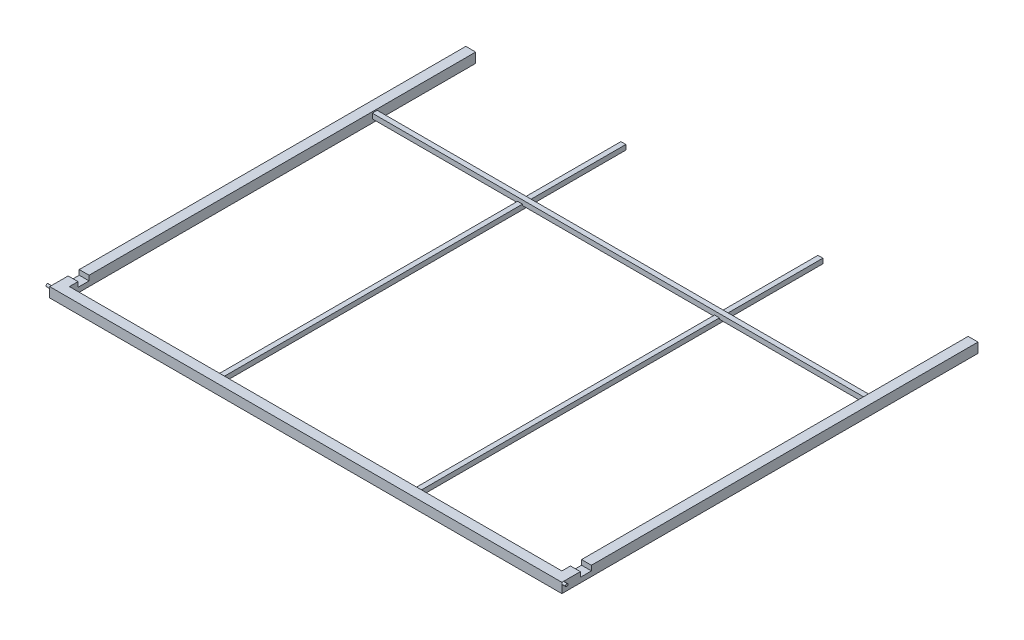
SolidWorks part; units mm, degrees
material "2014-T4"
ref_plane "Front Plane" through (0, 0, 0) normal (0, 0, 1) x (1, 0, 0)
ref_plane "Top Plane" through (0, 0, 0) normal (0, 1, 0) x (1, 0, 0)
ref_plane "Right Plane" through (0, 0, 0) normal (1, 0, 0) x (0, 0, -1)
sketch "Sketch1" plane through (0, 0, 0) normal (0, 1, 0) x (1, 0, 0)
  line L0 (1308.1, -1066.8) -> (1308.1, 1066.8)
  line L2 (-1308.1, 1066.8) -> (-1308.1, -1066.8)
  line L3 (-1308.1, -1066.8) -> (1308.1, -1066.8)
  line L5 (-1308.1, 1066.8) -> (1308.1, -1066.8) construction
  line L6 (-1308.1, -1066.8) -> (1308.1, 1066.8) construction
  point P0 (0, 0)
  dimension "D1" = 2133.6
  dimension "D2" = 2616.2
sketch "Sketch2" plane through (0, 0, 0) normal (0, 0, 1) x (1, 0, 0)
  line L0 (-1308.1, 0) -> (1308.1, 0) construction
  line L1 (-1320.8, 25.4) -> (-1270, 25.4)
  line L2 (-1320.8, 25.4) -> (-1320.8, -25.4)
  line L3 (-1320.8, -25.4) -> (-1270, -25.4)
  line L4 (-1270, 25.4) -> (-1270, -25.4)
  line L5 (-1320.8, 25.4) -> (-1270, -25.4) construction
  line L6 (-1320.8, -25.4) -> (-1270, 25.4) construction
  line L7 (-1308.1, 0) -> (1308.1, 0) construction
  line L8 (-1273.175, 22.225) -> (-1273.175, -22.225)
  line L9 (-1317.625, -22.225) -> (-1273.175, -22.225)
  line L10 (-1317.625, 22.225) -> (-1317.625, -22.225)
  line L11 (-1317.625, 22.225) -> (-1273.175, 22.225)
  point P0 (-1295.4, 0)
  dimension "D1" = 50.8
  dimension "D2" = 50.8
  dimension "D4" = 1295.4
  dimension "D3" = 3.175
sweep "Sweep1" add profiles "Sketch2" path "Sketch1"
sketch "Sketch6" plane through (-1320.8, 0, 0) normal (-1, 0, 0) x (0, 0, 1)
  line L1 (1079.5, 25.4) -> (-1066.8, 25.4) construction
  line L2 (1079.5, -25.4) -> (1079.5, 25.4) construction
  circle A0 centre (1073.15, 19.05) radius 6.35
  dimension "D3" = 12.7
  dimension "D1" = 6.35
  dimension "D2" = 6.35
extrude "Boss-Extrude3" add sketch "Sketch6" along normal blind 19.05
sketch "Sketch12" plane through (1320.8, 0, 0) normal (1, 0, 0) x (0, 0, -1)
  line L0 (-1079.5, -25.4) -> (-1079.5, 25.4) construction
  line L1 (-1079.5, 25.4) -> (1066.8, 25.4) construction
  circle A0 centre (-1073.15, 19.05) radius 6.35
  dimension "D1" = 12.7
extrude "Boss-Extrude6" add sketch "Sketch12" along normal blind 19.05 contours A0
ref_plane "Plane1" through (0, 0, 1073.15) normal (0, 0, 1) x (1, 0, 0)
sketch "Sketch7" plane through (0, 0, 1073.15) normal (0, 0, 1) x (1, 0, 0)
  line L0 (1422.4, 19.05) -> (-1422.4, 19.05) construction
  line L1 (-1320.8, -25.4) -> (-1320.8, 19.05) construction
  line L2 (1320.8, -25.4) -> (1320.8, 19.05) construction
  dimension "D1" = 6.35
  dimension "D2" = 101.6
  dimension "D3" = 101.6
sketch "Sketch13" plane through (-1320.8, 0, 0) normal (-1, 0, 0) x (0, 0, 1)
  line L0 (-1066.8, 25.4) -> (1073.15, 25.4) construction
  line L1 (927.1, 25.4) -> (984.25, 25.4)
  line L2 (927.1, 25.4) -> (927.1, 0)
  line L3 (927.1, 0) -> (984.25, 0)
  line L4 (984.25, 25.4) -> (984.25, 0)
  line L5 (927.1, 25.4) -> (984.25, 0) construction
  line L6 (927.1, 0) -> (984.25, 25.4) construction
  line L7 (1079.5, -25.4) -> (1079.5, 19.05) construction
  point P0 (955.675, 12.7)
  dimension "D1" = 57.15
  dimension "D2" = 25.4
  dimension "D3" = 152.4
extrude "Cut-Extrude2" cut sketch "Sketch13" against normal up to surface (2641.6 mm away) up to face at (1320.8, 2.277, 218.177)
sketch "Sketch14" plane through (1270, 0, 0) normal (-1, 0, 0) x (0, 0, 1)
  line L1 (-558.8, 19.05) -> (-533.4, 19.05)
  line L2 (-558.8, 19.05) -> (-558.8, -6.35)
  line L3 (-558.8, -6.35) -> (-533.4, -6.35)
  line L4 (-533.4, 19.05) -> (-533.4, -6.35)
  line L5 (-558.8, 19.05) -> (-533.4, -6.35) construction
  line L6 (-558.8, -6.35) -> (-533.4, 19.05) construction
  line L7 (-1066.8, -25.4) -> (-1066.8, 25.4) construction
  line L8 (-555.625, 15.875) -> (-555.625, -3.175)
  line L9 (-555.625, -3.175) -> (-536.575, -3.175)
  line L10 (-536.575, 15.875) -> (-536.575, -3.175)
  line L11 (-555.625, 15.875) -> (-536.575, 15.875)
  line L12 (1028.7, -25.4) -> (-1066.8, -25.4) construction
  point P0 (-546.1, 6.35)
  dimension "D1" = 25.4
  dimension "D2" = 25.4
  dimension "D3" = 508
  dimension "D5" = 19.05
  dimension "D4" = 3.175
extrude "Boss-Extrude7" add sketch "Sketch14" along normal up to surface (2540 mm away) separate body up to face at (-1270, 6.35, 468.3125)
sketch "Sketch16" plane through (0, 0, -558.8) normal (0, 0, -1) x (-1, 0, 0)
  line L0 (-1270, 19.05) -> (-1270, -6.35) construction
  line L1 (-520.7, 0) -> (-495.3, 0)
  line L2 (-520.7, 0) -> (-520.7, -6.35)
  line L3 (-520.7, -6.35) -> (-495.3, -6.35)
  line L4 (-495.3, 0) -> (-495.3, -6.35)
  line L5 (-520.7, 0) -> (-495.3, -6.35) construction
  line L6 (-520.7, -6.35) -> (-495.3, 0) construction
  line L7 (1270, -6.35) -> (-1270, -6.35) construction
  line L8 (495.3, 0) -> (495.3, -6.35)
  line L9 (495.3, 0) -> (520.7, 0)
  line L10 (520.7, 0) -> (520.7, -6.35)
  line L11 (495.3, -6.35) -> (520.7, -6.35)
  line L12 (1270, -6.35) -> (1270, 19.05) construction
  point P0 (-508, -3.175)
  point P9 (508, 0)
  dimension "D1" = 6.35
  dimension "D2" = 25.4
  dimension "D3" = 762
  dimension "D5" = 762
  dimension "D4" = 2
extrude "Cut-Extrude3" cut sketch "Sketch16" against normal up to surface (25.4 mm away) up to face at (0, 6.35, -533.4)
sketch "Sketch15" plane through (0, 0, 1028.7) normal (0, 0, -1) x (-1, 0, 0)
  line L0 (1270, -25.4) -> (-1270, -25.4) construction
  line L1 (-520.7, 0) -> (-495.3, 0)
  line L2 (-520.7, 0) -> (-520.7, -25.4)
  line L3 (-520.7, -25.4) -> (-495.3, -25.4)
  line L4 (-495.3, 0) -> (-495.3, -25.4)
  line L5 (-520.7, 0) -> (-495.3, -25.4) construction
  line L6 (-520.7, -25.4) -> (-495.3, 0) construction
  line L7 (-1270, 25.4) -> (-1270, -25.4) construction
  line L8 (-517.525, -3.175) -> (-517.525, -22.225)
  line L9 (-517.525, -22.225) -> (-498.475, -22.225)
  line L10 (-498.475, -3.175) -> (-498.475, -22.225)
  line L11 (-517.525, -3.175) -> (-498.475, -3.175)
  line L12 (498.475, -3.175) -> (498.475, -22.225)
  line L13 (498.475, -22.225) -> (517.525, -22.225)
  line L14 (517.525, -3.175) -> (517.525, -22.225)
  line L15 (498.475, -3.175) -> (517.525, -3.175)
  line L16 (495.3, 0) -> (495.3, -25.4)
  line L17 (495.3, 0) -> (520.7, 0)
  line L18 (520.7, 0) -> (520.7, -25.4)
  line L19 (495.3, -25.4) -> (520.7, -25.4)
  line L20 (1270, 25.4) -> (1270, -25.4) construction
  point P0 (-508, -12.7)
  point P23 (508, 0)
  dimension "D1" = 25.4
  dimension "D2" = 25.4
  dimension "D3" = 762
  dimension "D6" = 762
  dimension "D4" = 3.175
  dimension "D5" = 2
extrude "Boss-Extrude9" add sketch "Sketch15" along normal up to surface (2095.5 mm away) separate body up to face at (1295.4, 0, -1066.8)
sketch "Sketch17" plane through (1320.8, 0, 0) normal (1, 0, 0) x (0, 0, -1)
  line L0 (-984.25, 25.4) -> (-987.425, 25.4)
  line L1 (-1073.15, 25.4) -> (-984.25, 25.4) construction
  line L2 (-987.425, 25.4) -> (-987.425, -3.175)
  line L3 (-987.425, -3.175) -> (-923.925, -3.175)
  line L4 (-923.925, -3.175) -> (-923.925, 25.4)
  line L5 (-927.1, 25.4) -> (1066.8, 25.4) construction
  line L6 (-923.925, 25.4) -> (-927.1, 25.4)
  line L7 (-927.1, 25.4) -> (-927.1, 0)
  line L8 (-927.1, 0) -> (-984.25, 0)
  line L9 (-984.25, 0) -> (-984.25, 25.4)
  dimension "D1" = 3.175
  dimension "D2" = 3.175
  dimension "D3" = 3.175
extrude "Boss-Extrude10" add sketch "Sketch17" against normal up to surface (50.8 mm away) up to face at (1270, 6.35, 468.3125)
sketch "Sketch18" plane through (-1320.8, 0, 0) normal (-1, 0, 0) x (0, 0, 1)
  line L0 (927.1, 25.4) -> (923.925, 25.4)
  line L1 (-1066.8, 25.4) -> (927.1, 25.4) construction
  line L2 (923.925, 25.4) -> (923.925, -3.175)
  line L3 (923.925, -3.175) -> (987.425, -3.175)
  line L4 (987.425, -3.175) -> (987.425, 25.4)
  line L5 (984.25, 25.4) -> (1073.15, 25.4) construction
  line L6 (987.425, 25.4) -> (984.25, 25.4)
  line L7 (984.25, 25.4) -> (984.25, 0)
  line L8 (984.25, 0) -> (927.1, 0)
  line L9 (927.1, 0) -> (927.1, 25.4)
  dimension "D1" = 3.175
  dimension "D2" = 3.175
  dimension "D3" = 3.175
extrude "Boss-Extrude11" add sketch "Sketch18" against normal up to surface (50.8 mm away) up to face at (-1270, 6.35, 468.3125)
